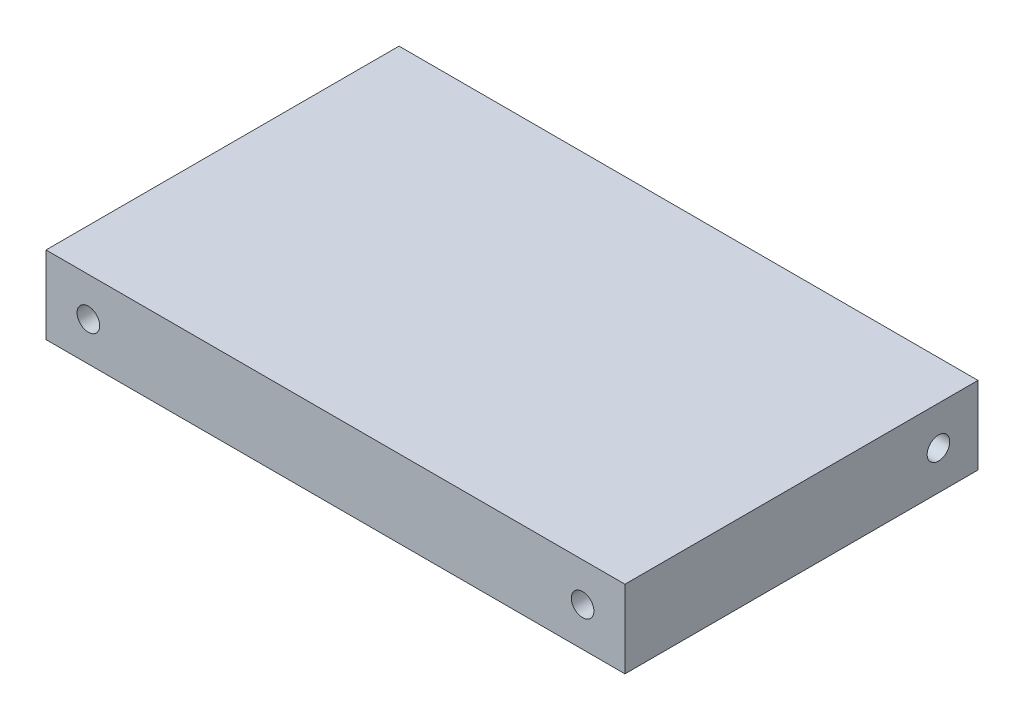
SolidWorks part; units mm, degrees
ref_plane "Płaszczyzna przednia" through (0, 0, 0) normal (0, 0, 1) x (1, 0, 0)
ref_plane "Płaszczyzna górna" through (0, 0, 0) normal (0, 1, 0) x (1, 0, 0)
ref_plane "Płaszczyzna prawa" through (0, 0, 0) normal (1, 0, 0) x (0, 0, -1)
sketch "Sketch1" plane through (0, 0, 0) normal (0, 0, 1) x (1, 0, 0)
  line L1 (0, 0) -> (-82, 0)
  line L2 (0, 0) -> (0, 11)
  line L3 (0, 11) -> (-82, 11)
  line L4 (-82, 0) -> (-82, 11)
  line L5 (0, 0) -> (-82, 11) construction
  line L6 (0, 11) -> (-82, 0) construction
  point P4 (-41, 5.5)
  dimension "D1" = 11
  dimension "D2" = 82
extrude "Boss-Extrude1" add sketch "Sketch1" along normal blind 50
sketch "Sketch2" plane through (0, 0, 0) normal (1, 0, 0) x (0, 0, -1)
  line L0 (0, 0) -> (0, 11) construction
  line L1 (-50, 0) -> (0, 0) construction
  circle A0 centre (-5.6, 5.5) radius 1.6
  dimension "D1" = 3.2
  dimension "D2" = 5.6
  dimension "D3" = 5.5
extrude "Cut-Extrude1" cut sketch "Sketch2" against normal blind 10
sketch "Sketch3" plane through (-82, 0, 0) normal (-1, 0, 0) x (0, 0, 1)
  line L0 (0, 11) -> (0, 0) construction
  line L1 (50, 11) -> (0, 11) construction
  circle A0 centre (5.6, 5.5) radius 1.6
  point P4 (0, 5.5)
  dimension "D1" = 3.2
  dimension "D2" = 5.6
  dimension "D3" = 5.5
extrude "Cut-Extrude2" cut sketch "Sketch3" against normal blind 10
sketch "Sketch4" plane through (0, 0, 50) normal (0, 0, 1) x (1, 0, 0)
  line L0 (0, 11) -> (-82, 11) construction
  line L1 (-82, 11) -> (-82, 0) construction
  line L2 (0, 0) -> (0, 11) construction
  circle A0 centre (-76, 5.5) radius 1.6
  circle A1 centre (-6, 5.5) radius 1.6
  dimension "D1" = 3.2
  dimension "D2" = 3.2
  dimension "D3" = 5.5
  dimension "D4" = 5.5
  dimension "D5" = 6
  dimension "D6" = 6
extrude "Cut-Extrude3" cut sketch "Sketch4" against normal blind 15
